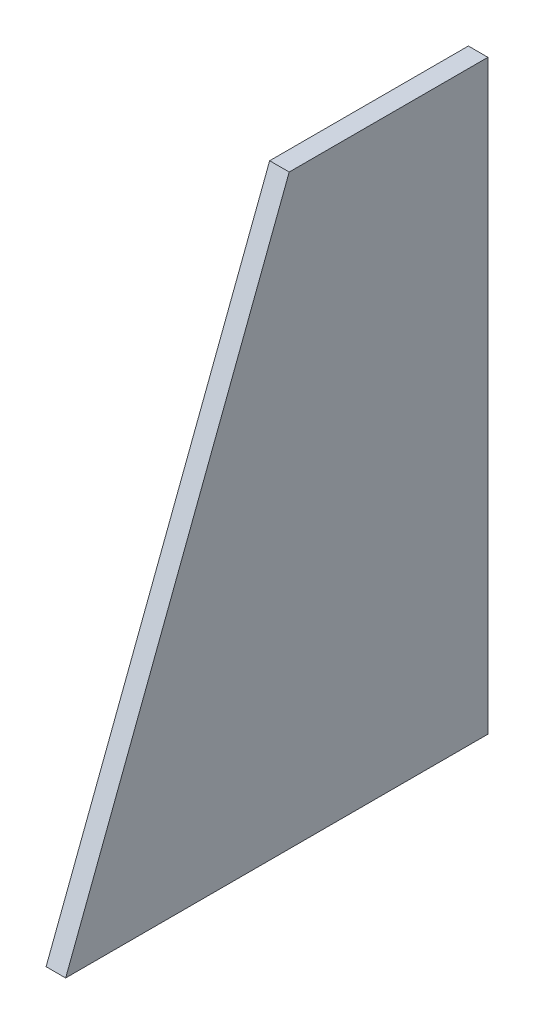
SolidWorks part; units mm, degrees
ref_plane "Front Plane" through (0, 0, 0) normal (0, 0, 1) x (1, 0, 0)
ref_plane "Top Plane" through (0, 0, 0) normal (0, 1, 0) x (1, 0, 0)
ref_plane "Right Plane" through (0, 0, 0) normal (1, 0, 0) x (0, 0, -1)
sketch "Sketch1" plane through (0, 0, 0) normal (1, 0, 0) x (0, 0, -1)
  line L0 (0, 149.86) -> (0, 0)
  line L1 (0, 0) -> (-107.95, 0)
  line L2 (-107.95, 0) -> (-50.8, 149.86)
  line L3 (-50.8, 149.86) -> (0, 149.86)
  point P4 (0, 0)
  dimension "D1" = 149.86
  dimension "D2" = 107.95
  dimension "D3" = 50.8
extrude "Boss-Extrude1" add sketch "Sketch1" along normal mid plane 5
